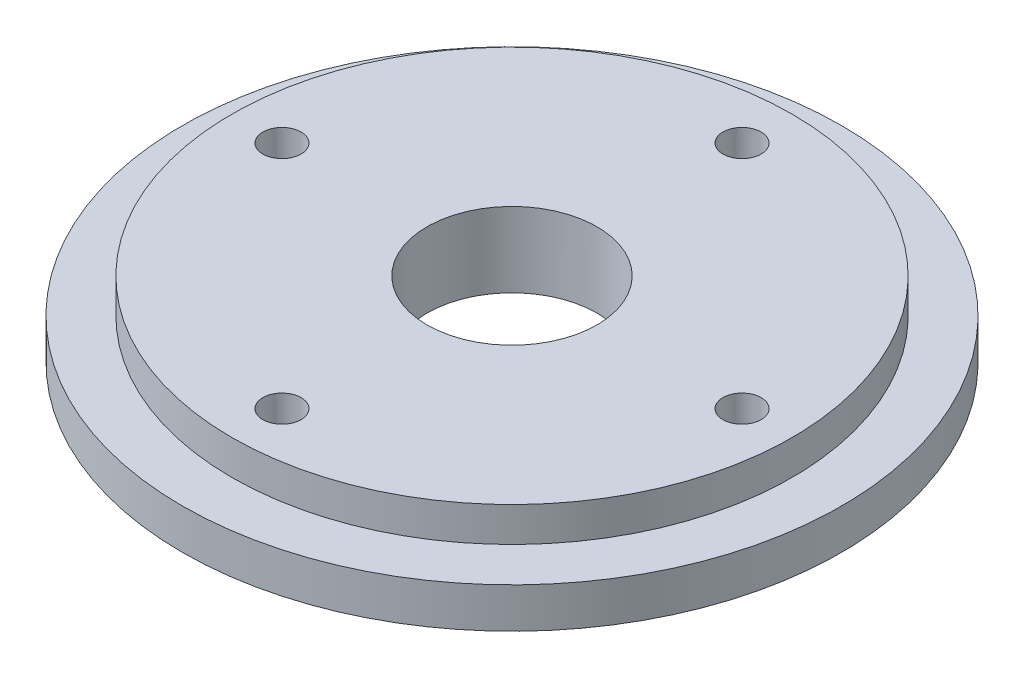
SolidWorks part; units mm, degrees
ref_plane "Front Plane" through (0, 0, 0) normal (0, 0, 1) x (1, 0, 0)
ref_plane "Top Plane" through (0, 0, 0) normal (0, 1, 0) x (1, 0, 0)
ref_plane "Right Plane" through (0, 0, 0) normal (1, 0, 0) x (0, 0, -1)
sketch "Sketch1" plane through (0, 0, 0) normal (0, 0, 1) x (1, 0, 0)
  line L0 (0, 0) -> (0, 11.35) construction
  line L1 (0, 0) -> (50, 0)
  line L2 (50, 0) -> (50, 6.1)
  line L3 (50, 6.1) -> (42.5, 6.1)
  line L4 (42.5, 6.1) -> (42.5, 11.35)
  line L5 (42.5, 11.35) -> (0, 11.35)
  line L6 (0, 0) -> (0, 11.35)
  dimension "D1" = 11.35
  dimension "D2" = 6.1
  dimension "D3" = 100
  dimension "D4" = 85
revolve "Revolve1" add sketch "Sketch1" angle 360 about L0
sketch "Sketch2" plane through (0, 11.35, 0) normal (0, 1, 0) x (1, 0, 0)
  line L0 (0, 12.9) -> (0, 32) construction
  line L1 (12.9, 0) -> (32, 0) construction
  line L2 (0, -12.9) -> (0, -32) construction
  line L3 (-12.9, 0) -> (-32, 0) construction
  circle A0 centre (0, 0) radius 12.9
  circle A1 centre (0, 0) radius 34.9 construction
  circle A2 centre (0, 34.9) radius 2.9
  circle A3 centre (34.9, 0) radius 2.9
  circle A4 centre (0, -34.9) radius 2.9
  circle A5 centre (-34.9, 0) radius 2.9
  dimension "D1" = 19.1
  dimension "D2" = 5.8
  dimension "D3" = 25.8
extrude "Cut-Extrude1" cut sketch "Sketch2" against normal up to next
